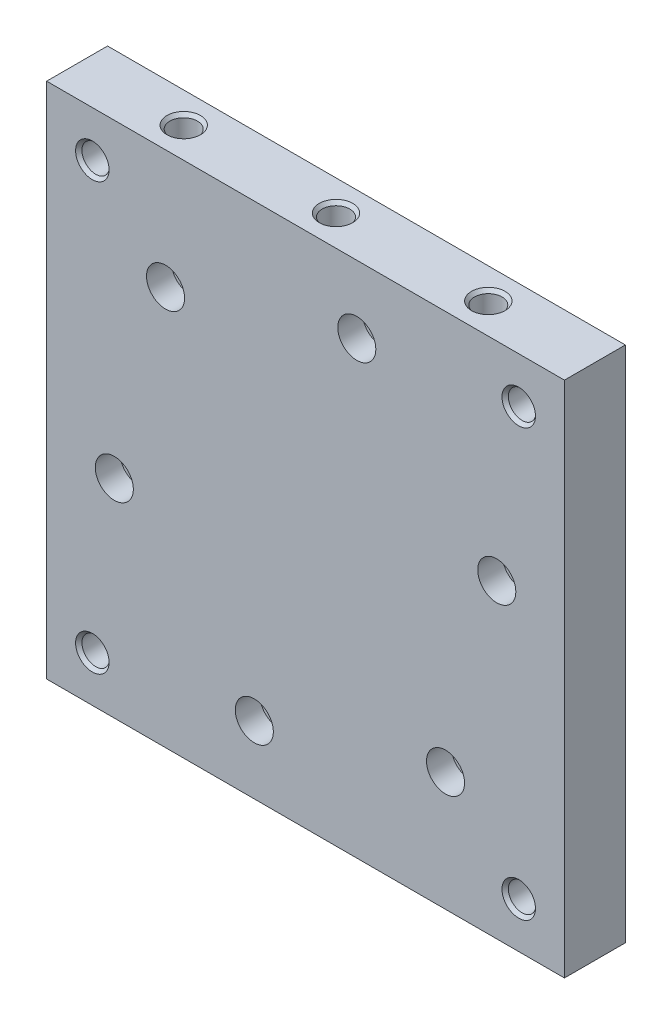
SolidWorks part; units mm, degrees
material "AISI 1018 Steel, Cold Rolled"
ref_plane "Front" through (0, 0, 0) normal (0, 0, 1) x (1, 0, 0)
ref_plane "Top" through (0, 0, 0) normal (0, 1, 0) x (1, 0, 0)
ref_plane "Right" through (0, 0, 0) normal (1, 0, 0) x (0, 0, -1)
sketch "Sketch1" plane through (0, 0, 0) normal (0, 0, 1) x (1, 0, 0)
  line L0 (0, 0) -> (0, 107.95) construction
  line L1 (-107.95, 107.95) -> (107.95, 107.95)
  line L2 (-107.95, 107.95) -> (-107.95, -107.95)
  line L3 (-107.95, -107.95) -> (107.95, -107.95)
  line L4 (107.95, 107.95) -> (107.95, -107.95)
  line L5 (0, 0) -> (107.95, 0) construction
  dimension "D1" = 215.9
  dimension "D2" = 215.9
extrude "Boss-Extrude1" add sketch "Sketch1" along normal blind 25.4
hole_wizard "1/2-20 Tapped Hole1" positions "Sketch3" profile "Sketch2" tap size "1/2-20" standard "Ansi Inch" end condition through all
sketch "Sketch3" plane through (0, 0, 25.4) normal (0, 0, 1) x (1, 0, 0)
  line L0 (-88.9, 88.9) -> (88.9, 88.9) construction
  line L1 (-88.9, 88.9) -> (-88.9, -88.9) construction
  line L2 (-88.9, -88.9) -> (88.9, -88.9) construction
  line L3 (88.9, 88.9) -> (88.9, -88.9) construction
  line L4 (0, 0) -> (0, 88.9) construction
  line L5 (0, 0) -> (88.9, 0) construction
  point P0 (-88.9, -88.9)
  point P1 (88.9, 88.9)
  point P3 (-88.9, 88.9)
  point P5 (88.9, -88.9)
  dimension "D1" = 177.8
  dimension "D2" = 177.8
sketch "Sketch2" plane through (-88.9, -88.9, 25.4) normal (1, 0, 0) x (0, -1, 0)
  line L0 (0, 0) -> (0, 25.4)
  line L1 (0, 25.4) -> (5.7544, 25.4)
  line L2 (5.7544, 25.4) -> (5.7544, 1.4157)
  line L3 (5.7544, 1.4157) -> (6.985, 0)
  line L5 (6.985, 0) -> (0, 0)
  line L6 (-5.7544, 1.4157) -> (-6.985, 0) construction
  line L11 (0, -6.35) -> (0, 107.95) construction
  dimension "Thru Tap Drill Dia." = 11.5087
  dimension "Thru Tap Drill Depth" = 25.4
  dimension "Near C'Sink Dia." = 13.97
  dimension "Near C'Sink Angle" = 82
cosmetic thread "Hole Thread1" parameters "D2"=12.7
cosmetic thread "Hole Thread2" parameters "D2"=12.7
cosmetic thread "Hole Thread3" parameters "D2"=12.7
cosmetic thread "Hole Thread4" parameters "D2"=12.7
hole_wizard "CBORE for 3/8 Socket Head Cap Screw1" positions "Sketch5" profile "Sketch4" counterbore size "3/8" standard "Ansi Inch" end condition through all
sketch "Sketch5" plane through (0, 0, 25.4) normal (0, 0, 1) x (1, 0, 0)
  line L0 (0, 0) -> (-58.3717, 58.3717) construction
  line L1 (-88.9, 88.9) -> (-58.3717, 58.3717) construction
  line L2 (0, 0) -> (58.3717, -58.3717) construction
  line L3 (21.3655, 79.7372) -> (0, 0) construction
  line L4 (0, 0) -> (-21.3655, -79.7372) construction
  line L5 (0, 0) -> (79.7372, 21.3655) construction
  line L6 (0, 0) -> (-79.7372, -21.3655) construction
  point P0 (-58.3717, 58.3717)
  point P11 (-79.7372, -21.3655)
  point P13 (-21.3655, -79.7372)
  point P15 (58.3717, -58.3717)
  point P17 (79.7372, 21.3655)
  point P19 (21.3655, 79.7372)
  dimension "D1" = 82.55
  dimension "D2" = 60
  dimension "D3" = 60
sketch "Sketch4" plane through (-58.3717, 58.3717, 25.4) normal (1, 0, 0) x (0, -1, 0)
  line L0 (0, 0) -> (0, 25.4)
  line L1 (0, 25.4) -> (5.1562, 25.4)
  line L3 (5.1562, 25.4) -> (5.1562, 10.3124)
  line L4 (5.1562, 10.3124) -> (7.9375, 10.3124)
  line L5 (7.9375, 10.3124) -> (7.9375, 0)
  line L7 (7.9375, 0) -> (0, 0)
  line L11 (0, -6.35) -> (0, 107.95) construction
  dimension "Thru Hole Dia." = 10.3124
  dimension "Thru Hole Depth" = 25.4
  dimension "C'Bore Dia." = 15.875
  dimension "C'Bore Depth" = 10.3124
hole_wizard "1/2-20 Tapped Hole2" positions "Sketch7" profile "Sketch6" tap size "1/2-20" standard "Ansi Inch"
sketch "Sketch7" plane through (-107.95, 0, 0) normal (-1, 0, 0) x (0, 0, 1)
  line L0 (12.7, 0) -> (12.7, -63.5) construction
  line L1 (12.7, 0) -> (12.7, 63.5) construction
  line L2 (0, 0) -> (12.7, 0) construction
  line L3 (0, 107.95) -> (0, -107.95) construction
  point P0 (12.7, 0)
  point P1 (12.7, 63.5)
  point P3 (12.7, -63.5)
  dimension "D1" = 12.7
  dimension "D2" = 63.5
sketch "Sketch6" plane through (-107.95, 0, 12.7) normal (0, 1, 0) x (0, 0, 1)
  line L0 (0, 0) -> (0, 23.1426)
  line L1 (0, 23.1426) -> (5.7544, 19.685)
  line L2 (5.7544, 19.685) -> (5.7544, 1.4157)
  line L3 (5.7544, 1.4157) -> (6.985, 0)
  line L5 (6.985, 0) -> (0, 0)
  line L6 (-5.7544, 1.4157) -> (-6.985, 0) construction
  line L10 (0, 23.1426) -> (-5.7544, 19.685) construction
  line L11 (0, -6.35) -> (0, 107.95) construction
  dimension "Tap Drill Dia." = 11.5087
  dimension "Tap Drill Depth" = 19.685
  dimension "Near C'Sink Dia." = 13.97
  dimension "Near C'Sink Angle" = 82
  dimension "Drill Angle" = 118
cosmetic thread "Hole Thread5" parameters "D1"=15.875, "D2"=12.7
cosmetic thread "Hole Thread6" parameters "D1"=15.875, "D2"=12.7
cosmetic thread "Hole Thread7" parameters "D1"=15.875, "D2"=12.7
ref_axis "Axis1" through (0, 0, -1.27) along (0, 0, 1)
pattern_circular "CirPattern1" count 2 over 90 about axis through (0, 0, -1.27) along (0, 0, 1) of "1/2-20 Tapped Hole2"
